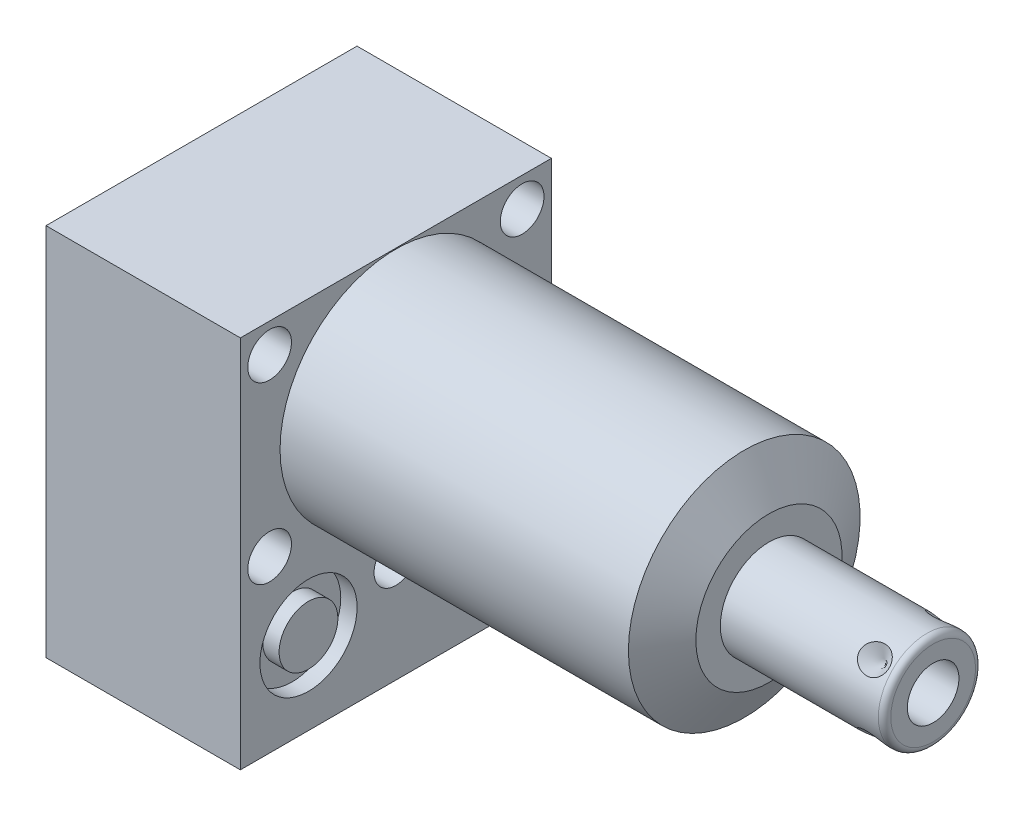
SolidWorks part; units mm, degrees
material "Alloy Steel"
ref_plane "Front Plane" through (0, 0, 0) normal (0, 0, 1) x (1, 0, 0)
ref_plane "Top Plane" through (0, 0, 0) normal (0, 1, 0) x (1, 0, 0)
ref_plane "Right Plane" through (0, 0, 0) normal (1, 0, 0) x (0, 0, -1)
ref_plane "Plane1" through (0, 0, 0) normal (1, 0, 0) x (0, 0, -1)
sketch "Sketch1" plane through (0, 0, 0) normal (1, 0, 0) x (0, 0, -1)
  line L0 (-25.4, 19.05) -> (-25.4, -42.0624)
  line L1 (-25.4, -42.0624) -> (25.4, -42.0624)
  line L2 (25.4, -42.0624) -> (25.4, 19.05)
  line L3 (25.4, 19.05) -> (-25.4, 19.05)
  line L4 (0, -47.0916) -> (0, 22.1996) construction
  dimension "D1" = 50.8
  dimension "D2" = 61.1124
  dimension "D3" = 19.05
extrude "Extrude1" add sketch "Sketch1" along normal blind 60.9346 and the other way blind 31.75
ref_plane "Plane2" through (0, 0, 0) normal (1, 0, 0) x (0, 0, -1)
sketch "Sketch2" plane through (0, 0, 0) normal (1, 0, 0) x (0, 0, -1)
  line L0 (-20.8153, 0) -> (20.8153, 0) construction
  line L6 (25.4, 19.05) -> (-25.4, 19.05)
  line L7 (-25.4, 19.05) -> (-25.4, -42.0624)
  line L8 (-25.4, -42.0624) -> (25.4, -42.0624)
  line L9 (25.4, -42.0624) -> (25.4, 19.05)
  line L10 (25.4, 19.05) -> (-25.4, 19.05)
  line L11 (-25.4, 19.05) -> (-25.4, -42.0624)
  line L12 (-25.4, -42.0624) -> (25.4, -42.0624)
  line L13 (25.4, -42.0624) -> (25.4, 19.05)
  circle A0 centre (0, 0) radius 18.923
  dimension "D1" = 37.846
  dimension "D2" = 0
extrude "Cut-Extrude1" cut sketch "Sketch2" along normal up to next
ref_plane "Plane3" through (0, 0, 0) normal (0, 0, 1) x (1, 0, 0)
sketch "Sketch3" plane through (0, 0, 0) normal (0, 0, 1) x (1, 0, 0)
  line L0 (56.9018, 18.923) -> (60.9346, 11.938)
  line L1 (56.7002, 0) -> (61.1362, 0) construction
  line L2 (60.9346, 18.923) -> (60.9346, 11.938)
  line L3 (60.9346, 18.923) -> (56.9018, 18.923)
  line L4 (60.9346, 18.923) -> (0, 18.923) construction
  line L5 (60.9346, -18.923) -> (60.9346, 18.923) construction
  dimension "D1" = 23.876
  dimension "D2" = 30
revolve "Cut-Revolve1" cut sketch "Sketch3" angle 360 about L1
ref_plane "Plane4" through (-29.083, -28.575, 14.2748) normal (0, 0, 1) x (0, 1, 0)
sketch "S2D0002" plane through (-29.083, -28.575, 14.2748) normal (0, 0, 1) x (0, 1, 0)
  line L0 (0, 0) -> (4.5466, 0)
  line L1 (4.5466, 0) -> (4.1066, -2.0701)
  line L2 (4.1066, -2.0701) -> (3.4544, -2.7223)
  line L3 (3.4544, -2.7223) -> (3.4544, -13.97)
  line L4 (3.4544, -13.97) -> (0, -13.97)
  line L5 (0, -13.97) -> (0, 0)
  line L6 (0, -14.6685) -> (0, 0.6985) construction
  dimension "D1" = 13.97
revolve "Cut-Revolve2" cut sketch "S2D0002" angle 360 about L6
ref_plane "Plane5" through (-29.083, -28.575, -14.2748) normal (0, 0, 1) x (0, 1, 0)
sketch "Sketch5" plane through (-29.083, -28.575, -14.2748) normal (0, 0, 1) x (0, 1, 0)
  line L0 (0, 0) -> (4.5466, 0)
  line L1 (4.5466, 0) -> (4.1066, -2.0701)
  line L2 (4.1066, -2.0701) -> (3.4544, -2.7223)
  line L3 (3.4544, -2.7223) -> (3.4544, -13.97)
  line L4 (3.4544, -13.97) -> (0, -13.97)
  line L5 (0, -13.97) -> (0, 0)
  line L6 (0, -14.6685) -> (0, 0.6985) construction
  dimension "D1" = 13.97
revolve "Cut-Revolve3" cut sketch "Sketch5" angle 360 about L6
ref_plane "Plane6" through (-2.667, -28.575, 14.2748) normal (0, 0, 1) x (0, -1, 0)
sketch "Sketch6" plane through (-2.667, -28.575, 14.2748) normal (0, 0, 1) x (0, -1, 0)
  line L0 (0, 0) -> (4.5466, 0)
  line L1 (4.5466, 0) -> (4.1066, -2.0701)
  line L2 (4.1066, -2.0701) -> (3.4544, -2.7223)
  line L3 (3.4544, -2.7223) -> (3.4544, -12.192)
  line L4 (3.4544, -12.192) -> (0, -12.192)
  line L5 (0, -12.192) -> (0, 0)
  line L6 (0, -12.8016) -> (0, 0.6096) construction
  dimension "D1" = 12.192
revolve "Cut-Revolve4" cut sketch "Sketch6" angle 360 about L6
ref_plane "Plane7" through (-2.667, -28.575, -14.2748) normal (0, 0, 1) x (0, -1, 0)
sketch "Sketch7" plane through (-2.667, -28.575, -14.2748) normal (0, 0, 1) x (0, -1, 0)
  line L0 (0, 0) -> (4.5466, 0)
  line L1 (4.5466, 0) -> (4.1066, -2.0701)
  line L2 (4.1066, -2.0701) -> (3.4544, -2.7223)
  line L3 (3.4544, -2.7223) -> (3.4544, -12.192)
  line L4 (3.4544, -12.192) -> (0, -12.192)
  line L5 (0, -12.192) -> (0, 0)
  line L6 (0, -12.8016) -> (0, 0.6096) construction
  dimension "D1" = 12.192
revolve "Cut-Revolve5" cut sketch "Sketch7" angle 360 about L6
ref_plane "Plane8" through (-15.875, -43.688, 14.2748) normal (0, 0, 1) x (-1, 0, 0)
sketch "Sketch18" plane through (-31.75, 0, 0) normal (-1, 0, 0) x (0, 0, 1)
  circle A0 centre (-14.2748, -28.575) radius 7.9375
  circle A1 centre (14.2748, -28.575) radius 7.9375
  dimension "D1" = 15.875
  dimension "D2" = 15.875
extrude "Cut-Extrude2" cut sketch "Sketch18" against normal blind 2.667
sketch "Sketch19" plane through (0, 0, 0) normal (1, 0, 0) x (0, 0, -1)
  circle A0 centre (-14.2748, -28.575) radius 7.9375
  circle A1 centre (14.2748, -28.575) radius 7.9375
  dimension "D1" = 15.875
  dimension "D2" = 15.875
extrude "Cut-Extrude3" cut sketch "Sketch19" against normal blind 2.667
sketch "Sketch8" plane through (-15.875, -43.688, 14.2748) normal (0, 0, 1) x (-1, 0, 0)
  line L0 (0, -1.8796) -> (6.1849, -1.8796)
  line L1 (6.1849, -1.8796) -> (5.6423, -4.4323)
  line L2 (5.6423, -4.4323) -> (4.9784, -5.0962)
  line L3 (4.9784, -5.0962) -> (4.9784, -20.9296)
  line L4 (4.9784, -20.9296) -> (0, -20.9296)
  line L5 (0, -20.9296) -> (0, -1.8796)
  line L6 (0, -26.67) -> (0, 1.27) construction
  line L7 (15.875, -1.6256) -> (-15.875, -1.6256) construction
  dimension "D1" = 19.05
  dimension "D2" = 0.254
revolve "Cut-Revolve6" cut sketch "Sketch8" angle 360 about L6
ref_plane "Plane9" through (-15.875, -43.688, -14.2748) normal (0, 0, 1) x (-1, 0, 0)
sketch "Sketch9" plane through (-15.875, -43.688, -14.2748) normal (0, 0, 1) x (-1, 0, 0)
  line L0 (0, -1.8796) -> (6.1849, -1.8796)
  line L1 (6.1849, -1.8796) -> (5.6423, -4.4323)
  line L2 (5.6423, -4.4323) -> (4.9784, -5.0962)
  line L3 (4.9784, -5.0962) -> (4.9784, -20.9296)
  line L4 (4.9784, -20.9296) -> (0, -20.9296)
  line L5 (0, -20.9296) -> (0, -1.8796)
  line L6 (0, -26.67) -> (0, 1.27) construction
  line L7 (15.875, -1.6256) -> (-15.875, -1.6256) construction
  dimension "D1" = 19.05
  dimension "D2" = 0.254
revolve "Cut-Revolve7" cut sketch "Sketch9" angle 360 about L6
ref_plane "Plane10" through (0, 0, 0) normal (0, 0, 1) x (1, 0, 0)
sketch "Sketch20" plane through (0, -42.0624, 0) normal (0, -1, 0) x (1, 0, 0)
  circle A0 centre (-15.875, 14.2748) radius 9.525
  circle A1 centre (-15.875, -14.2748) radius 9.525
  dimension "D1" = 19.05
extrude "Cut-Extrude4" cut sketch "Sketch20" against normal blind 0.254
sketch "Sketch10" plane through (0, 0, 0) normal (0, 0, 1) x (1, 0, 0)
  line L0 (60.9346, 0) -> (60.9346, 7.9375)
  line L1 (60.9346, 7.9375) -> (86.741, 7.9375)
  line L2 (87.757, 6.9215) -> (87.757, 0)
  line L3 (87.757, 0) -> (60.9346, 0)
  line L4 (59.5935, 0) -> (89.0981, 0) construction
  line L5 (60.9346, -11.938) -> (60.9346, 11.938) construction
  line L6 (-31.75, 19.05) -> (-31.75, -42.0624) construction
  arc A0 (87.757, 6.9215) -> (86.741, 7.9375) centre (86.741, 6.9215) ccw
  point P0 (60.9346, 0)
  dimension "D2" = 1.016
  dimension "D1" = 15.875
  dimension "D3" = 119.507
revolve "Revolve1" add sketch "Sketch10" angle 360 about L4
ref_plane "Plane11" through (87.757, -4.2164, 0) normal (0, 0, 1) x (0, -1, 0)
sketch "S2D0001" plane through (87.757, -4.2164, 0) normal (0, 0, 1) x (0, -1, 0)
  line L0 (0, 0) -> (0, -15.24)
  line L1 (0, -15.24) -> (-4.2164, -17.7735)
  line L2 (0, 0) -> (-4.2164, 0)
  line L3 (-4.2164, 0) -> (-4.2164, -17.7735)
  line L4 (-4.2164, -24.865) -> (-4.2164, 0.8887) construction
  line L5 (2.7051, 0) -> (-11.1379, 0) construction
  dimension "D1" = 8.4328
  dimension "D2" = 59
  dimension "D3" = 15.24
revolve "Cut-Revolve8" cut sketch "S2D0001" angle 360 about L4
ref_plane "Plane12" through (-31.75, -43.688, 0) normal (0, -1, 0) x (0, 0, -1)
sketch "Sketch12" plane through (-31.75, -41.8084, 0) normal (0, -1, 0) x (0, 0, -1)
  circle A0 centre (-14.2748, 15.875) radius 6.4389
  circle A1 centre (-14.2748, 15.875) radius 9.525 construction
  dimension "D1" = 12.8778
extrude "Extrude2" add sketch "Sketch12" along normal blind 1.651
sketch "Sketch13" plane through (0, 0, 0) normal (1, 0, 0) x (0, 0, -1)
  circle A0 centre (-14.2748, -28.575) radius 4.8006
  circle A1 centre (-14.2748, -28.575) radius 4.5466 construction
  dimension "D1" = 9.6012
ref_plane "Plane13" through (-31.75, 0, 0) normal (1, 0, 0) x (0, 0, -1)
extrude "Extrude3" add sketch "Sketch13" along normal up to surface (2.667 mm away)
ref_plane "Plane14" through (0, -28.575, -14.2748) normal (0, -1, 0) x (0, 0, -1)
sketch "Sketch14" plane through (0, -28.575, -14.2748) normal (0, -1, 0) x (0, 0, -1)
  line L0 (0, -2.8435) -> (0, 1.0401) construction
  line L1 (0, -2.667) -> (0, -4.7371) construction
  line L2 (7.9375, -2.667) -> (-7.9375, -2.667) construction
  circle A0 centre (6.1722, -0.9017) radius 1.7653
  dimension "D1" = 3.5306
  dimension "D2" = 12.3444
revolve "Revolve2" add sketch "Sketch14" angle 360 about L0
ref_plane "Plane15" through (0, -28.575, -14.2748) normal (0, -1, 0) x (0, 0, -1)
sketch "Sketch15" plane through (0, -28.575, -14.2748) normal (0, -1, 0) x (0, 0, -1)
  line L0 (0, -32.7901) -> (0, -28.9065) construction
  line L1 (0, -26.3607) -> (0, -19.4599) construction
  line L2 (-7.9375, -29.083) -> (7.9375, -29.083) construction
  circle A0 centre (6.1722, -30.8483) radius 1.7653
  dimension "D1" = 3.5306
  dimension "D2" = 12.3444
revolve "Revolve3" add sketch "Sketch15" angle 360 about L0
ref_plane "Plane16" through (83.7946, -7.9375, 0) normal (0, 0, 1) x (-1, 0, 0)
ref_plane "Plane17" through (0, 0, 0) normal (0, 0.7071, 0.7071) x (-1, 0, 0)
sketch "Sketch16" plane through (83.7946, 5.6127, -5.6127) normal (0, -0.7071, -0.7071) x (-1, 0, 0)
  line L0 (0, 0) -> (2.413, 0)
  line L1 (2.413, 0) -> (0, -2.413)
  line L2 (0, 0) -> (0, -2.413)
  line L3 (0, -3.8054) -> (0, 0.1207) construction
  line L4 (22.86, 0) -> (-2.9464, 0) construction
  line L5 (-3.9624, -1.016) -> (-3.9624, -14.859) construction
  dimension "D1" = 3.9624
  dimension "D2" = 4.826
  dimension "D3" = 45
revolve "Cut-Revolve9" cut sketch "Sketch16" angle 360 about L3
pattern_circular "CirPattern1" count 4 over 360 about axis through (60.9356, 0, 0) along (-1, 0, 0) of "Cut-Revolve9"
hole_wizard "Hole1" positions "Sketch22" profile "Sketch21" legacy end condition up to next
sketch "Sketch22" plane through (0, 0, 0) normal (1, 0, 0) x (0, 0, -1)
  line L0 (0, 0) -> (-32.1908, 0) construction
  point P0 (-20.6248, 14.2748)
  point P1 (0, -25.0952)
  point P13 (-20.6248, -14.2748)
  point P14 (20.6248, 14.2748)
  point P15 (20.6248, -14.2748)
  dimension "D2" = 14.2748
  dimension "D3" = 25.0952
sketch "Sketch21" plane through (0, 14.2748, 20.6248) normal (0, 1, 0) x (0, 0, -1)
  line L0 (0, 0) -> (0, 31.75)
  line L1 (0, 31.75) -> (3.5687, 31.75)
  line L2 (3.5687, 31.75) -> (3.5687, 0)
  line L3 (3.5687, 0) -> (0, 0)
  line L4 (0, 110) -> (0, -10) construction
  dimension "Diameter" = 7.1374
  dimension "Depth" = 31.75
sketch "Sketch24" plane through (-29.083, 0, 0) normal (-1, 0, 0) x (0, 0, 1)
  circle A0 centre (14.2748, -28.575) radius 4.8006
  dimension "D1" = 9.6012
extrude "Extrude4" add sketch "Sketch24" along normal blind 2.667
